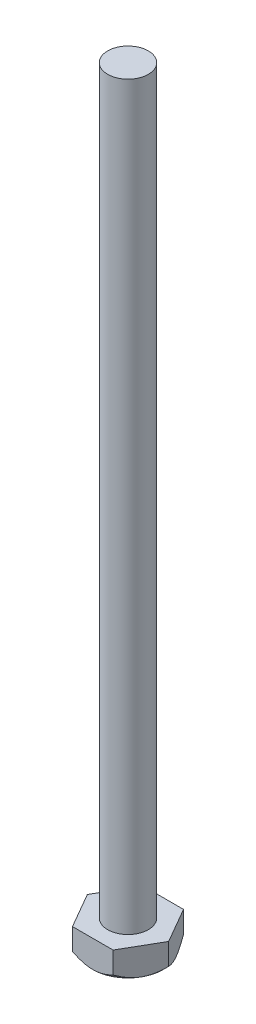
SolidWorks part; units mm, degrees
material "2024 Alloy"
ref_plane "Front Plane" through (0, 0, 0) normal (0, 0, 1) x (1, 0, 0)
ref_plane "Top Plane" through (0, 0, 0) normal (0, 1, 0) x (1, 0, 0)
ref_plane "Right Plane" through (0, 0, 0) normal (1, 0, 0) x (0, 0, -1)
sketch "Sketch1" plane through (0, 0, 0) normal (0, 1, 0) x (1, 0, 0)
  line L1 (-4.5, 0) -> (-2.25, -3.8971)
  line L2 (-2.25, -3.8971) -> (2.25, -3.8971)
  line L3 (2.25, -3.8971) -> (4.5, 0)
  line L4 (4.5, 0) -> (2.25, 3.8971)
  line L5 (2.25, 3.8971) -> (-2.25, 3.8971)
  line L6 (-2.25, 3.8971) -> (-4.5, 0)
  circle A0 centre (0, 0) radius 3.8971 construction
  dimension "D1" = 9
extrude "Boss-Extrude1" add sketch "Sketch1" along normal blind 3
sketch "Sketch2" plane through (0, 3, 0) normal (0, 1, 0) x (1, 0, 0)
  circle A0 centre (0, 0) radius 2.25
  dimension "D1" = 4.5
extrude "Boss-Extrude2" add sketch "Sketch2" along normal blind 82
cosmetic thread "Cosmetic Thread1" parameters "D2"=3.22
sketch "Sketch4" plane through (0, 0, 0) normal (1, 0, 0) x (0, 0, -1)
  line L0 (3.8971, 0) -> (4.8971, 1)
  line L1 (4.8971, 1) -> (4.8971, 0)
  line L2 (4.8971, 0) -> (3.8971, 0)
  line L3 (0, 0) -> (0, 50000) construction
  dimension "D1" = 45
  dimension "D2" = 1
revolve "Cut-Revolve1" cut sketch "Sketch4" angle 360 about L3
